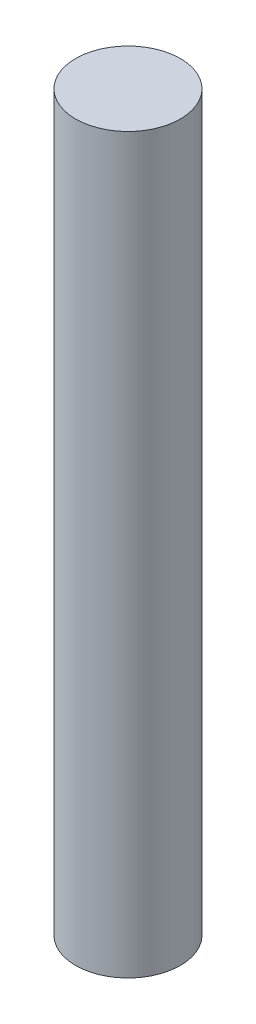
SolidWorks part; units mm, degrees
ref_plane "Front Plane" through (0, 0, 0) normal (0, 0, 1) x (1, 0, 0)
ref_plane "Top Plane" through (0, 0, 0) normal (0, 1, 0) x (1, 0, 0)
ref_plane "Right Plane" through (0, 0, 0) normal (1, 0, 0) x (0, 0, -1)
sketch "Sketch1" plane through (0, 0, 0) normal (0, 1, 0) x (1, 0, 0)
  circle A0 centre (0, 0) radius 2.5
  dimension "D1" = 5
extrude "Boss-Extrude1" add sketch "Sketch1" along normal blind 35 contours A0
move or copy body "Body-Move/Copy1" [suppressed] bodies to move or copy 101
